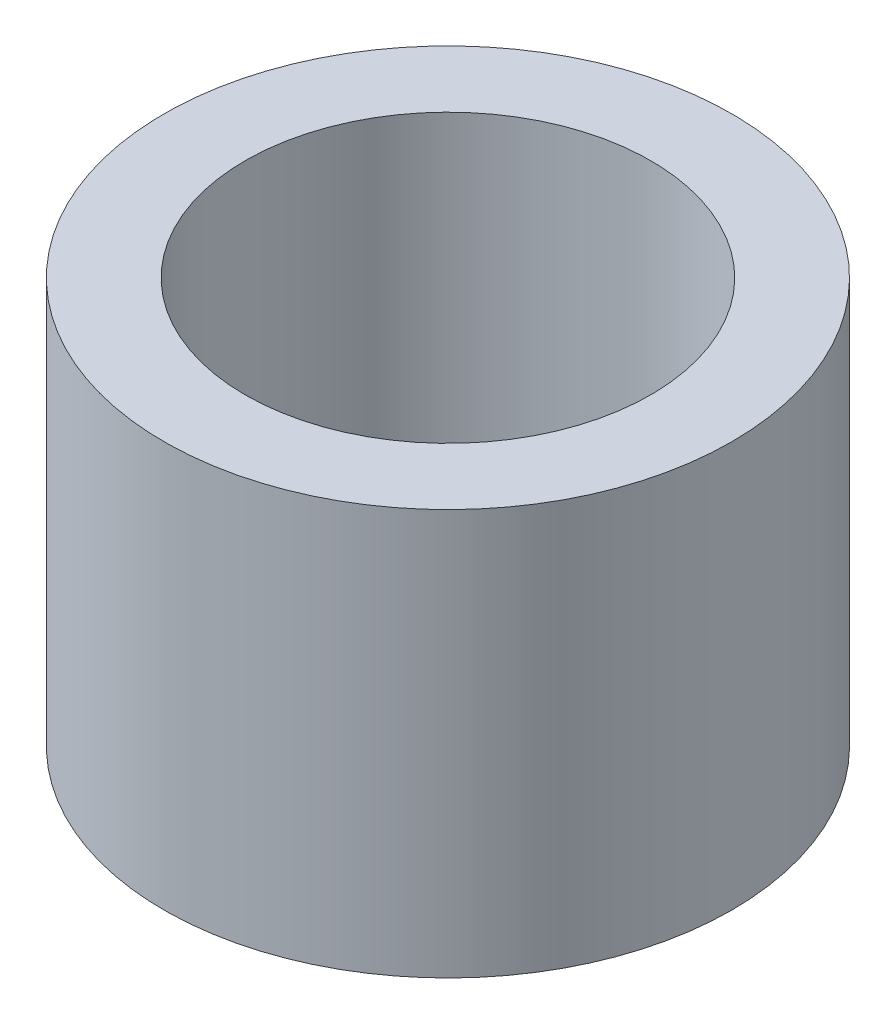
SolidWorks part; units mm, degrees
material "Простая углеродистая сталь"
ref_plane "Спереди" through (0, 0, 0) normal (0, 0, 1) x (1, 0, 0)
ref_plane "Сверху" through (0, 0, 0) normal (0, 1, 0) x (1, 0, 0)
ref_plane "Справа" through (0, 0, 0) normal (1, 0, 0) x (0, 0, -1)
sketch "Эскиз1" plane through (0, 0, 0) normal (0, 1, 0) x (1, 0, 0)
  circle A0 centre (0, 0) radius 25
extrude "Вытянуть-Тонкостенный1" add sketch "Эскиз1" along normal blind 50 thin
